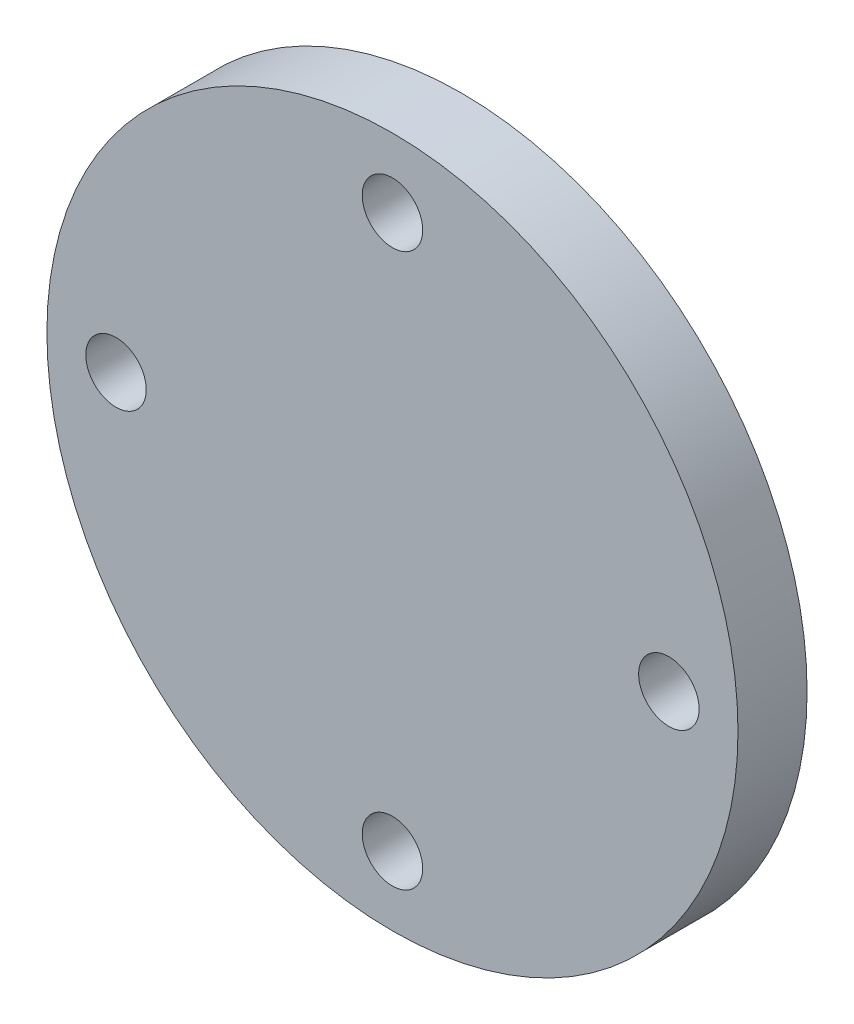
SolidWorks part; units mm, degrees
material "Cast Carbon Steel"
ref_plane "Front Plane" through (0, 0, 0) normal (0, 0, 1) x (1, 0, 0)
ref_plane "Top Plane" through (0, 0, 0) normal (0, 1, 0) x (1, 0, 0)
ref_plane "Right Plane" through (0, 0, 0) normal (1, 0, 0) x (0, 0, -1)
sketch "Sketch1" plane through (0, 0, 0) normal (0, 0, 1) x (1, 0, 0)
  circle A0 centre (0, 0) radius 63.5
  circle A2 centre (-50.8, 0) radius 5.5562
  circle A3 centre (0, 50.8) radius 5.5562
  circle A4 centre (50.8, 0) radius 5.5562
  circle A5 centre (0, -50.8) radius 5.5562
  point P15 (0, 0)
  dimension "D1" = 127
  dimension "D2" = 50.8
  dimension "D3" = 11.1125
  dimension "D4" = 4
extrude "Boss-Extrude1" add sketch "Sketch1" along normal blind 12.7
sketch "Sketch2" plane through (0, 0, 0) normal (0, 0, -1) x (-1, 0, 0)
  line L3 (-2.413, 7.5618) -> (-2.413, 3.1115)
  line L4 (-2.413, 3.1115) -> (2.413, 3.1115)
  line L5 (2.413, 3.1115) -> (2.413, 7.5618)
  circle A0 centre (0, 0) radius 12.7
  arc A1 (-2.413, 7.5618) -> (2.413, 7.5618) centre (0, 0) ccw
  dimension "D1" = 25.4
  dimension "D2" = 15.875
  dimension "D3" = 4.4503
  dimension "D4" = 4.826
  dimension "D5" = 4.4503
extrude "Boss-Extrude2" add sketch "Sketch2" along normal blind 35.56
